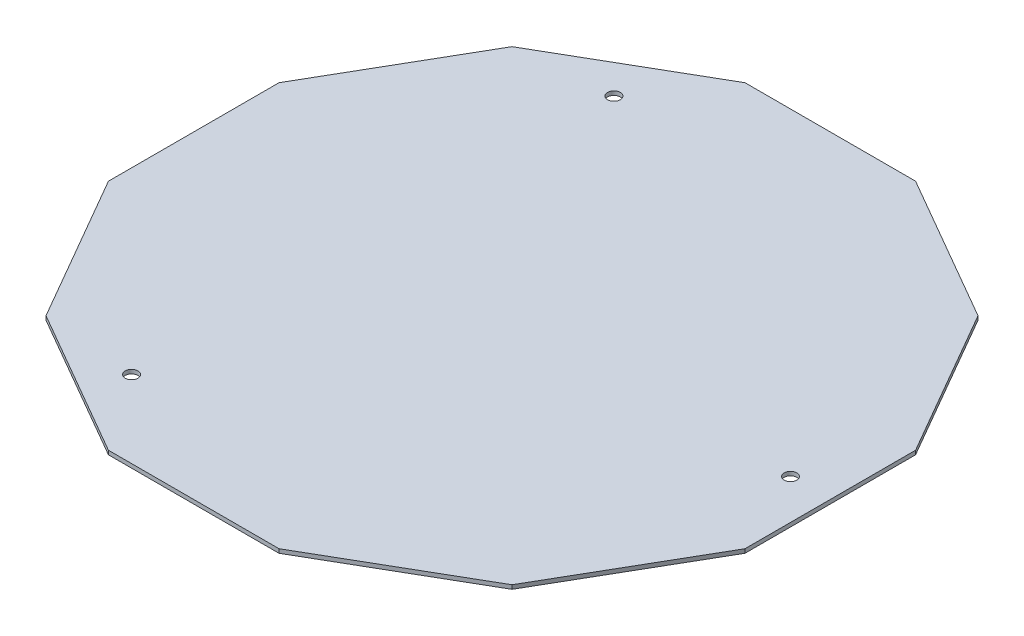
SolidWorks part; units mm, degrees
ref_plane "正面" through (0, 0, 0) normal (0, 0, 1) x (1, 0, 0)
ref_plane "平面" through (0, 0, 0) normal (0, 1, 0) x (1, 0, 0)
ref_plane "右側面" through (0, 0, 0) normal (1, 0, 0) x (0, 0, -1)
sketch "ｽｹｯﾁ1" plane through (0, 0, 0) normal (0, 1, 0) x (1, 0, 0)
  line L0 (-80, -21.4359) -> (-58.5641, -58.5641)
  line L1 (80, 21.4359) -> (58.5641, 58.5641)
  line L2 (58.5641, 58.5641) -> (21.4359, 80)
  line L3 (21.4359, 80) -> (-21.4359, 80)
  line L4 (-21.4359, 80) -> (-58.5641, 58.5641)
  line L5 (-58.5641, 58.5641) -> (-80, 21.4359)
  line L6 (-80, 21.4359) -> (-80, -21.4359)
  line L7 (-58.5641, -58.5641) -> (-21.4359, -80)
  line L8 (-21.4359, -80) -> (21.4359, -80)
  line L9 (21.4359, -80) -> (58.5641, -58.5641)
  line L10 (58.5641, -58.5641) -> (80, -21.4359)
  line L11 (80, -21.4359) -> (80, 21.4359)
  circle A0 centre (0, 0) radius 80 construction
extrude "ﾎﾞｽ - 押し出し1" add sketch "ｽｹｯﾁ1" along normal blind 1
sketch "ｽｹｯﾁ2" plane through (0, 1, 0) normal (0, 1, 0) x (1, 0, 0)
  circle A0 centre (-35, 60.6218) radius 1.6
extrude "ｶｯﾄ - 押し出し1" cut sketch "ｽｹｯﾁ2" against normal up to next
sketch "ｽｹｯﾁ3" plane through (0, 1, 0) normal (0, 1, 0) x (1, 0, 0)
  circle A0 centre (-35, -60.6218) radius 1.6
extrude "ｶｯﾄ - 押し出し2" cut sketch "ｽｹｯﾁ3" against normal up to next
sketch "ｽｹｯﾁ4" plane through (0, 1, 0) normal (0, 1, 0) x (1, 0, 0)
  circle A0 centre (70, 0) radius 1.6
extrude "ｶｯﾄ - 押し出し3" cut sketch "ｽｹｯﾁ4" against normal up to next
